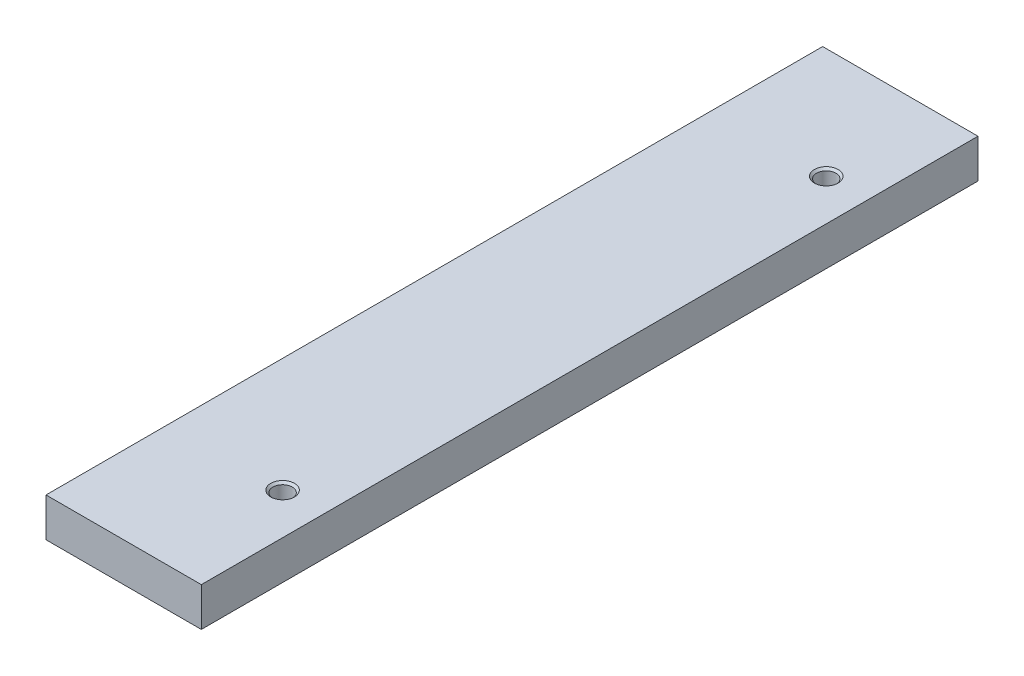
SolidWorks part; units mm, degrees
ref_plane "Front Plane" through (0, 0, 0) normal (0, 0, 1) x (1, 0, 0)
ref_plane "Top Plane" through (0, 0, 0) normal (0, 1, 0) x (1, 0, 0)
ref_plane "Right Plane" through (0, 0, 0) normal (1, 0, 0) x (0, 0, -1)
sketch "Sketch1" plane through (0, 0, 0) normal (0, 0, 1) x (1, 0, 0)
  line L1 (-10, -2.5) -> (10, -2.5)
  line L2 (-10, -2.5) -> (-10, 2.5)
  line L3 (-10, 2.5) -> (10, 2.5)
  line L4 (10, -2.5) -> (10, 2.5)
  line L5 (-10, -2.5) -> (10, 2.5) construction
  line L6 (-10, 2.5) -> (10, -2.5) construction
  point P0 (0, 0)
  dimension "D1" = 20
  dimension "D2" = 5
extrude "Boss-Extrude1" add sketch "Sketch1" along normal blind 100
sketch "Sketch7" plane through (0, 2.5, 0) normal (0, 1, 0) x (1, 0, 0)
  point P0 (4.6988, -14.2364)
hole_wizard "M3 Tapped Hole2" positions "Sketch7" profile "Sketch6" tap size "M3" standard "ISO" end condition through all
sketch "Sketch6" plane through (4.6988, 2.5, 14.2364) normal (1, 0, 0) x (0, 0, 1)
  line L0 (0, 0) -> (0, 5)
  line L1 (0, 5) -> (1.25, 5)
  line L2 (1.25, 5) -> (1.25, 0.275)
  line L3 (1.25, 0.275) -> (1.525, 0)
  line L5 (1.525, 0) -> (0, 0)
  line L6 (-1.25, 0.275) -> (-1.525, 0) construction
  line L11 (0, -6.35) -> (0, 107.95) construction
  dimension "Thru Tap Drill Dia." = 2.5
  dimension "Thru Tap Drill Depth" = 5
  dimension "Near C'Sink Dia." = 3.05
  dimension "Near C'Sink Angle" = 90
cosmetic thread "Hole Thread4" parameters "D2"=3
pattern_linear "LPattern1" count 2 spacing 70 along (0, 0, 1) of "M3 Tapped Hole2"
cosmetic thread "Hole Thread5" parameters "D2"=3
